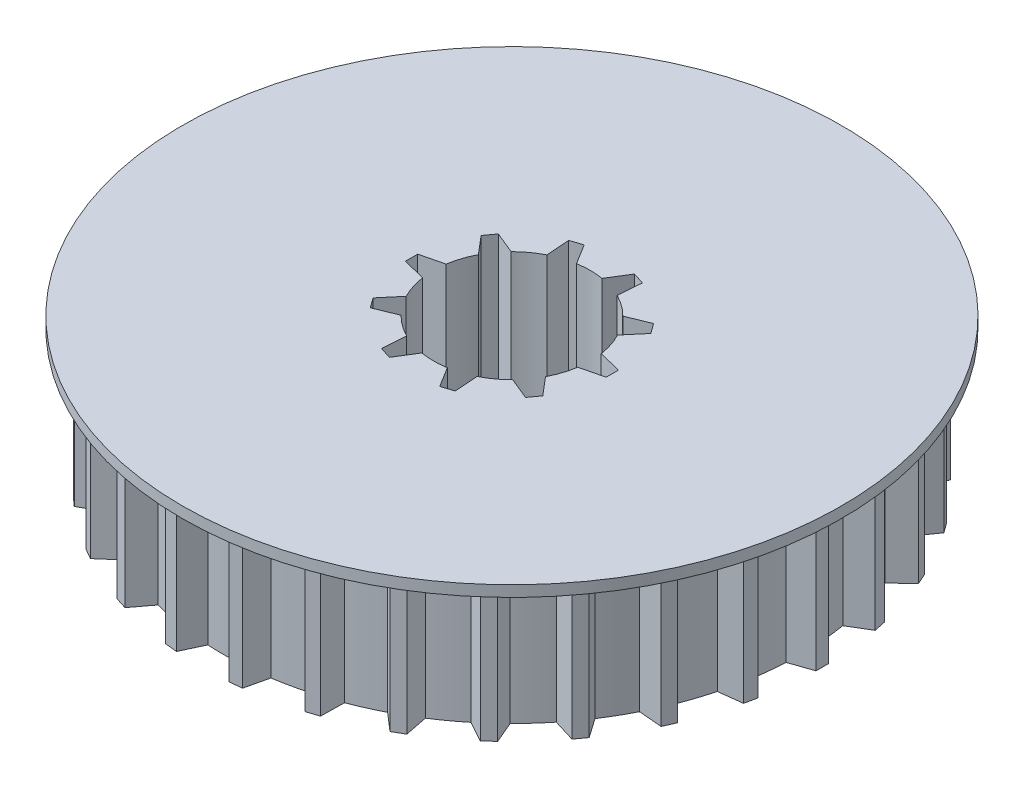
SolidWorks part; units mm, degrees
ref_plane "Front Plane" through (0, 0, 0) normal (0, 0, 1) x (1, 0, 0)
ref_plane "Top Plane" through (0, 0, 0) normal (0, 1, 0) x (1, 0, 0)
ref_plane "Right Plane" through (0, 0, 0) normal (1, 0, 0) x (0, 0, -1)
sketch "Sketch1" plane through (0, 0, 0) normal (0, 1, 0) x (1, 0, 0)
  line L3 (14.12, 0) -> (14.12, -0.28)
  line L4 (14.12, 0) -> (14.12, 0.28)
  line L5 (14.12, -0.28) -> (12.8499, -0.7184)
  line L6 (14.12, 0.28) -> (12.8499, 0.7184)
  circle A0 centre (0, 0) radius 13.12
  arc A3 (12.8499, -0.7184) -> (12.8499, 0.7184) centre (0, 0) ccw
  point P3 (12.87, 0)
  point P10 (14.12, 0)
  dimension "D1" = 26.24
  dimension "D2" = 12.87
  dimension "D5" = 14.12
  dimension "D6" = 0.28
  dimension "D7" = 0.28
  dimension "D8" = 1.3436
extrude "Boss-Extrude1" add sketch "Sketch1" along normal blind 6.3 contours L5 A3 L6 A0 | A3 L5 A0 L6 | A0 L5 L3 L4 L6
pattern_circular "CirPattern1" count 30 over 360 about axis through (0, 0, 0) along (0, 1, 0) of "Boss-Extrude1"
sketch "Sketch2" plane through (0, 6.3, 0) normal (0, 1, 0) x (1, 0, 0)
  circle A0 centre (0, 0) radius 15
  dimension "D1" = 30
extrude "Boss-Extrude2" add sketch "Sketch2" along normal blind 0.5
sketch "Sketch5" plane through (0, 0, 0) normal (0, -1, 0) x (1, 0, 0)
  line L0 (4.57, 0) -> (4.57, -0.28)
  line L1 (4.57, 0) -> (4.57, 0.28)
  line L2 (4.57, -0.28) -> (3.2654, -0.5999)
  line L3 (4.57, 0.28) -> (3.2654, 0.5999)
  circle A0 centre (0, 0) radius 3.57
  arc A1 (3.2654, -0.5999) -> (3.2654, 0.5999) centre (0, 0) ccw
  point P2 (3.32, 0)
  point P3 (4.57, 0)
  dimension "D1" = 7.14
  dimension "D2" = 3.32
  dimension "D3" = 4.57
  dimension "D4" = 0.28
  dimension "D5" = 0.28
  dimension "D6" = 1.3433
  dimension "D7" = 1.3433
  dimension "D8" = 0
  dimension "D9" = 0
extrude "Cut-Extrude2" cut sketch "Sketch5" against normal through all contours L2 A1 L3 A0 | A1 L2 A0 L3 | A0 L2 L0 L1 L3
pattern_circular "CirPattern2" count 10 over 360 about axis through (0, 0, 0) along (0, 1, 0) of "Cut-Extrude2"
